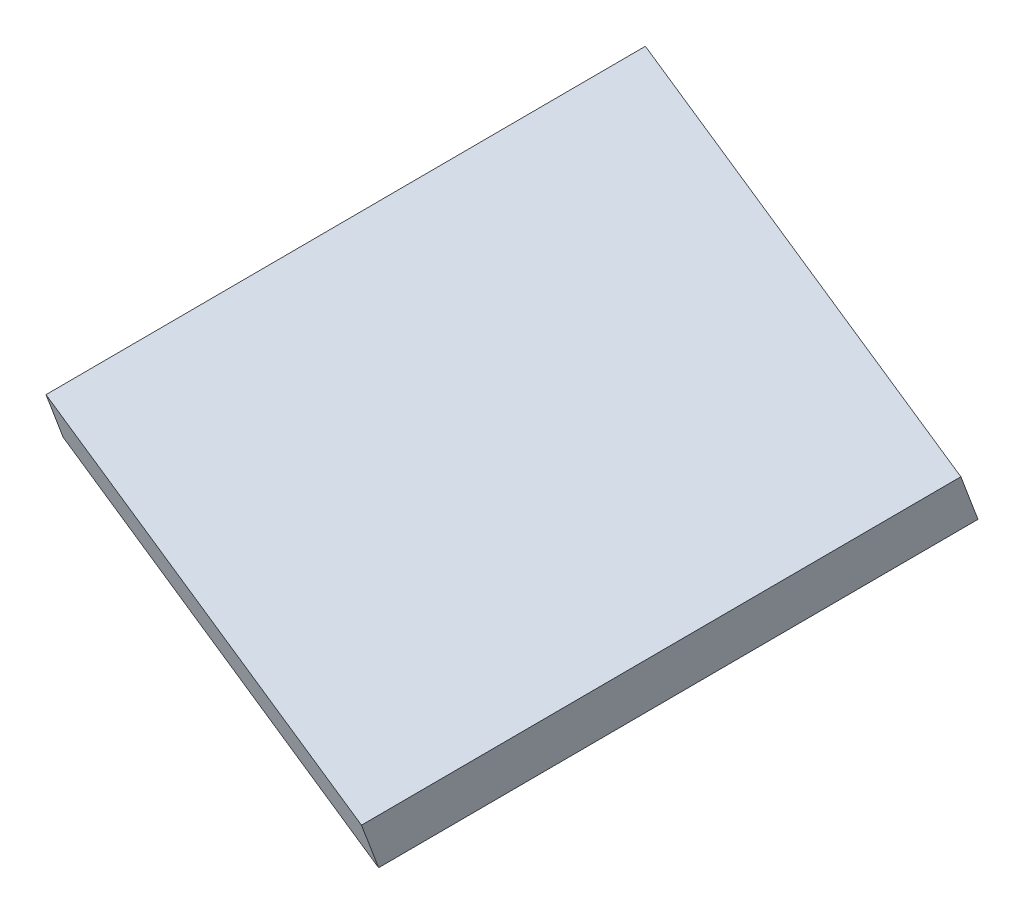
SolidWorks part; units mm, degrees
ref_plane "Front Plane" through (0, 0, 0) normal (0, 0, 1) x (1, 0, 0)
ref_plane "Top Plane" through (0, 0, 0) normal (0, 1, 0) x (1, 0, 0)
ref_plane "Right Plane" through (0, 0, 0) normal (1, 0, 0) x (0, 0, -1)
sketch "Sketch2" plane through (-485.0156, 24.0931, 406.7236) normal (0.0128, 0.933, 0.3598) x (-0.3313, -0.3355, 0.8818)
  line L0 (-264.1386, 198.8491) -> (-264.1386, 160.9804)
  line L3 (-314.1386, 148.8491) -> (-314.1386, 198.8491)
  line L4 (-314.1386, 198.8491) -> (-264.1386, 198.8491)
  line L6 (-264.1386, 148.8491) -> (-314.1386, 148.8491)
  line L12 (-264.1386, 160.9804) -> (-264.1386, 148.8491)
  point P11 (-314.1386, 173.8491)
  dimension "D3" = 50
  dimension "D4" = 50
extrude "Boss-Extrude1" add sketch "Sketch2" along normal blind 5
